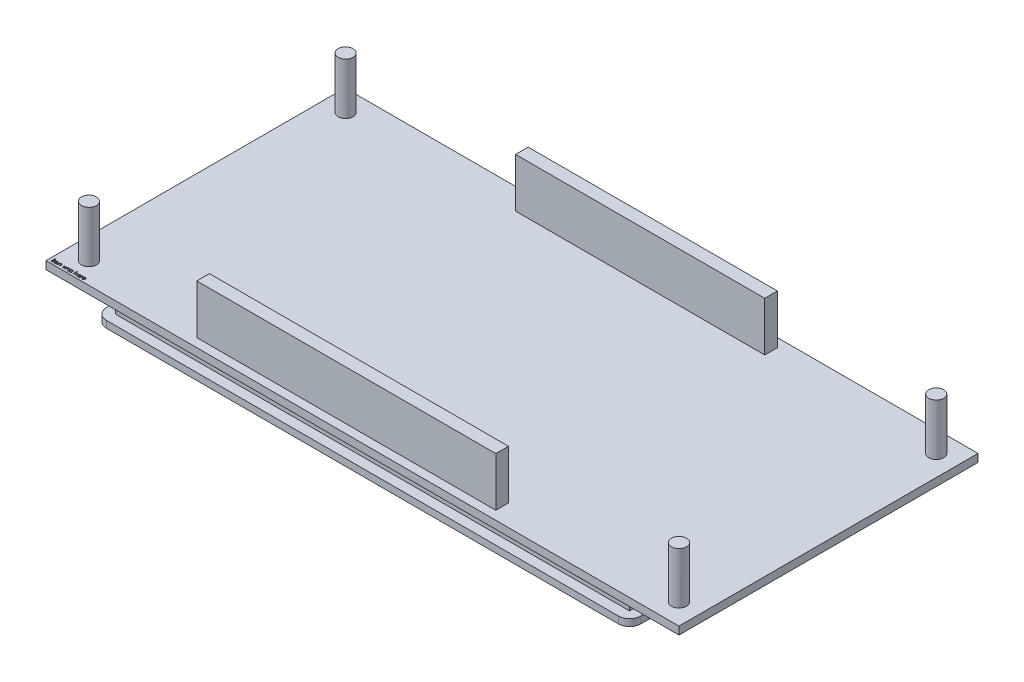
SolidWorks part; units mm, degrees
ref_plane "Front Plane" through (0, 0, 0) normal (0, 0, 1) x (1, 0, 0)
ref_plane "Top Plane" through (0, 0, 0) normal (0, 1, 0) x (1, 0, 0)
ref_plane "Right Plane" through (0, 0, 0) normal (1, 0, 0) x (0, 0, -1)
sketch "Sketch1" plane through (0, 0, 0) normal (0, 1, 0) x (1, 0, 0)
  line L1 (0, 0) -> (127, 0)
  line L2 (0, 0) -> (0, 60)
  line L3 (0, 60) -> (127, 60)
  line L4 (127, 0) -> (127, 60)
  dimension "D1" = 60
  dimension "D2" = 127
extrude "Boss-Extrude1" add sketch "Sketch1" along normal blind 1.57
sketch "Sketch2" plane through (0, 1.57, 0) normal (0, 1, 0) x (1, 0, 0)
  line L0 (127, 60) -> (0, 60) construction
  line L2 (0, 0) -> (127, 0) construction
  line L3 (127, 0) -> (127, 60) construction
  circle A0 centre (4.31, 55.81) radius 1.5
  circle A1 centre (4.31, 4.31) radius 1.5
  circle A2 centre (122.81, 4.19) radius 1.5
  circle A3 centre (122.81, 55.81) radius 1.5
  dimension "D1" = 3
  dimension "D2" = 3
  dimension "D3" = 3
  dimension "D4" = 3
  dimension "D5" = 51.5
  dimension "D6" = 118.5
  dimension "D7" = 118.5
  dimension "D9" = 4.19
  dimension "D10" = 4.19
  dimension "D11" = 4.19
  dimension "D12" = 4.19
extrude "Boss-Extrude2" add sketch "Sketch2" along direction (0, -1, 0) on the side of the normal blind 10.33
sketch "Sketch3" plane through (0, 0, 0) normal (0, -1, 0) x (1, 0, 0)
  line L0 (0, 0) -> (127, 0) construction
  line L1 (9.9, -60) -> (117.1, -60)
  line L2 (9.9, -60) -> (9.9, 0)
  line L3 (9.9, 0) -> (117.1, 0)
  line L4 (117.1, -60) -> (117.1, 0)
  line L5 (9.9, -60) -> (117.1, 0) construction
  line L6 (9.9, 0) -> (117.1, -60) construction
  line L7 (127, -60) -> (0, -60) construction
  line L8 (127, 0) -> (127, -60) construction
  line L9 (0, -60) -> (0, 0) construction
  line L10 (19.1711, -54.811) -> (107.8289, -5.189) construction
  line L11 (19.1711, -54.811) -> (107.8289, -54.811)
  line L12 (19.1711, -54.811) -> (19.1711, -5.189)
  line L13 (19.1711, -5.189) -> (107.8289, -5.189)
  line L14 (107.8289, -54.811) -> (107.8289, -5.189)
  line L15 (19.1711, -54.811) -> (107.8289, -5.189) construction
  line L16 (19.1711, -5.189) -> (107.8289, -54.811) construction
  point P0 (63.5, -30)
  point P13 (63.5, -30)
  dimension "D1" = 9.9
  dimension "D2" = 9.9
  dimension "D3" = 101.6
extrude "Boss-Extrude3" add sketch "Sketch3" along normal blind 4.13
sketch "Sketch4" plane through (0, 0, 0) normal (0, -1, 0) x (1, 0, 0)
  line L0 (11.9, -58) -> (11.9, -2)
  line L1 (9.9, -60) -> (117.1, -60)
  line L2 (9.9, -60) -> (9.9, 0)
  line L3 (9.9, 0) -> (117.1, 0)
  line L4 (117.1, -60) -> (117.1, 0)
  line L5 (11.9, -2) -> (115.1, -2)
  line L6 (115.1, -58) -> (115.1, -2)
  line L7 (11.9, -58) -> (115.1, -58)
  point P0 (63.5, -30)
  line M6 (9.9, -60) -> (9.9, 0)
  dimension "D1" = 2
extrude "Cut-Extrude1" cut sketch "Sketch4" along normal blind 2.75 contours L1 L4 L3 L7 L0 L5 L6 M6
fillet "Fillet1" radius 2.25 4 edges at (117.1, -3.44, -60) (117.1, -3.44, 0) (9.9, -3.44, 0) (9.9, -3.44, -60)
sketch "Sketch5" plane through (0, 0, 0) normal (0, -1, 0) x (1, 0, 0)
  line L4 (19.1711, -5.189) -> (19.1711, -54.811)
  line L5 (19.1711, -54.811) -> (107.8289, -54.811)
  line L6 (107.8289, -54.811) -> (107.8289, -5.189)
  line L7 (107.8289, -5.189) -> (19.1711, -5.189)
  line L8 (19.1711, -5.189) -> (19.1711, -54.811)
  line L9 (19.1711, -54.811) -> (107.8289, -54.811)
  line L10 (107.8289, -54.811) -> (107.8289, -5.189)
  line L11 (107.8289, -5.189) -> (19.1711, -5.189)
  dimension "D1" = 0
extrude "Boss-Extrude4" add sketch "Sketch5" along normal blind 4
sketch "Sketch6" plane through (0, 1.57, 0) normal (0, 1, 0) x (1, 0, 0)
  line L0 (127, 60) -> (0, 60) construction
  line L1 (38.5, 55.71) -> (88.5, 55.71)
  line L2 (38.5, 55.71) -> (38.5, 58.25)
  line L3 (38.5, 58.25) -> (88.5, 58.25)
  line L4 (88.5, 55.71) -> (88.5, 58.25)
  line L5 (38.5, 55.71) -> (88.5, 58.25) construction
  line L6 (38.5, 58.25) -> (88.5, 55.71) construction
  line L7 (28.5, 1.75) -> (88.5, 1.75)
  line L8 (28.5, 1.75) -> (28.5, 4.29)
  line L9 (28.5, 4.29) -> (88.5, 4.29)
  line L10 (88.5, 1.75) -> (88.5, 4.29)
  line L11 (28.5, 1.75) -> (88.5, 4.29) construction
  line L12 (28.5, 4.29) -> (88.5, 1.75) construction
  line L13 (0, 0) -> (127, 0) construction
  point P0 (63.5, 56.98)
  dimension "D1" = 2.54
  dimension "D2" = 50
  dimension "D3" = 63.5
  dimension "D4" = 1.75
  dimension "D5" = 2.54
  dimension "D6" = 60
  dimension "D7" = 1.75
extrude "Boss-Extrude5" add sketch "Sketch6" along normal blind 9.85
sketch "Sketch7" plane through (0, 1.57, 0) normal (0, 1, 0) x (1, 0, 0)
  text T0 "Ben was here" font "Century Gothic" height 0.75
extrude "Boss-Extrude6" add sketch "Sketch7" along normal blind 0.1
